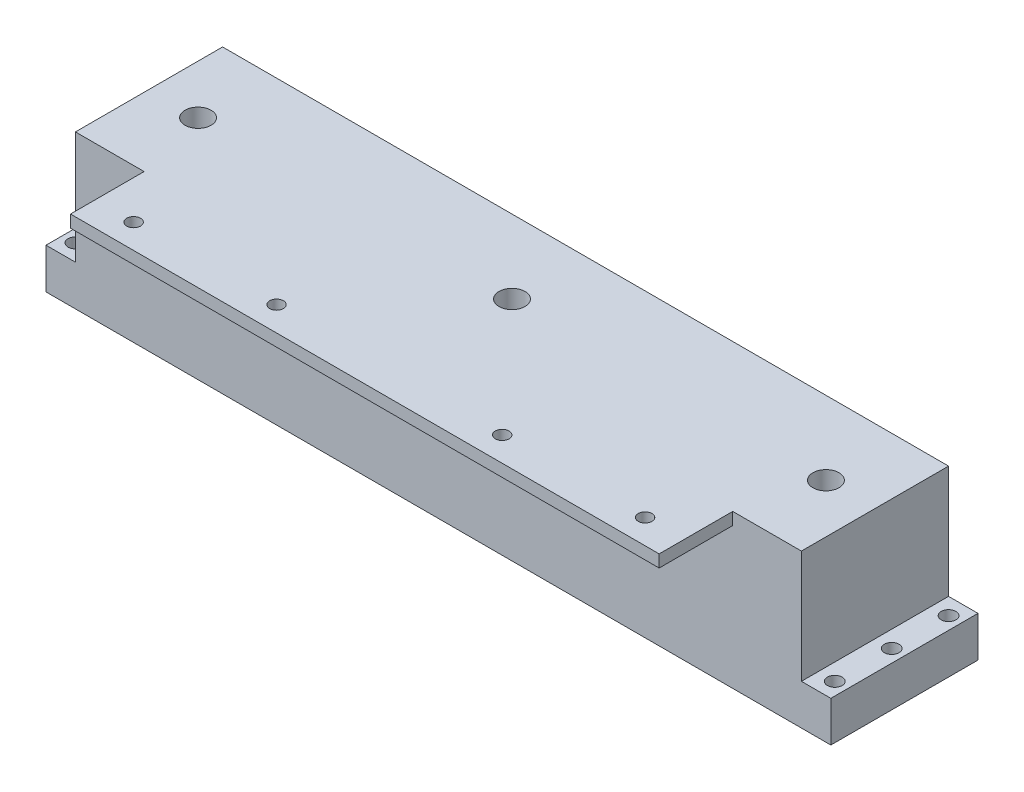
SolidWorks part; units mm, degrees
material "PPE"
ref_plane "Front Plane" through (0, 0, 0) normal (0, 0, 1) x (1, 0, 0)
ref_plane "Top Plane" through (0, 0, 0) normal (0, 1, 0) x (1, 0, 0)
ref_plane "Right Plane" through (0, 0, 0) normal (1, 0, 0) x (0, 0, -1)
sketch "Sketch1" plane through (0, 0, 0) normal (0, 1, 0) x (1, 0, 0)
  line L1 (-101.6, -19.05) -> (101.6, -19.05)
  line L2 (-101.6, -19.05) -> (-101.6, 19.05)
  line L3 (-101.6, 19.05) -> (101.6, 19.05)
  line L4 (101.6, -19.05) -> (101.6, 19.05)
  line L5 (-101.6, -19.05) -> (101.6, 19.05) construction
  line L6 (-101.6, 19.05) -> (101.6, -19.05) construction
  point P0 (0, 0)
  dimension "D1" = 203.2
  dimension "D2" = 38.1
extrude "Boss-Extrude1" add sketch "Sketch1" along normal blind 39.6926
sketch "Sketch3" plane through (0, 0, 0) normal (0, -1, 0) x (1, 0, 0)
  line L0 (-101.6, 0) -> (-60.6691, 0) construction
  line L1 (-101.6, -19.05) -> (-101.6, 19.05) construction
  line L2 (-98.298, 19.05) -> (-98.298, -19.05) construction
  line L3 (-101.6, 19.05) -> (101.6, 19.05) construction
  line L4 (101.6, -19.05) -> (-101.6, -19.05) construction
  circle A0 centre (-98.298, 14.732) radius 1.905
  circle A1 centre (-98.298, 0) radius 1.905
  circle A2 centre (-98.298, -14.732) radius 1.905
  dimension "D2" = 3.81
  dimension "D3" = 3.81
  dimension "D5" = 3.81
  dimension "D1" = 14.732
  dimension "D4" = 3.302
  dimension "D6" = 14.732
extrude "Cut-Extrude1" cut sketch "Sketch3" against normal through all
mirror "Mirror1" about plane through (0, 0, 0) normal (1, 0, 0) of "Cut-Extrude1"
sketch "Sketch4" plane through (0, 39.6926, 0) normal (0, 1, 0) x (1, 0, 0)
  line L0 (101.6, -19.05) -> (101.6, 19.05) construction
  line L1 (101.6, 19.05) -> (-101.6, 19.05) construction
  line L2 (0, 0) -> (0, -19.05) construction
  circle A1 centre (0, 0) radius 3.3782
  circle A2 centre (81.28, 0) radius 3.3782
  circle A3 centre (-81.28, 0) radius 3.3782
  dimension "D1" = 101.6
  dimension "D2" = 6.7564
  dimension "D5" = 6.7564
  dimension "D3" = 20.32
  dimension "D4" = 19.05
  dimension "D6" = 19.05
extrude "Cut-Extrude3" cut sketch "Sketch4" against normal through all
sketch "Sketch6" plane through (0, 0, 0) normal (0, -1, 0) x (1, 0, 0)
  line L0 (0, 19.05) -> (0, -19.05) construction
  line L1 (-101.6, 19.05) -> (101.6, 19.05) construction
  line L2 (101.6, -19.05) -> (-101.6, -19.05) construction
  line L3 (101.6, 19.05) -> (101.6, -19.05) construction
  line L4 (86.995, 3.2996) -> (81.28, 6.5991)
  line L5 (81.28, 6.5991) -> (75.565, 3.2996)
  line L6 (75.565, 3.2996) -> (75.565, -3.2996)
  line L7 (75.565, -3.2996) -> (81.28, -6.5991)
  line L8 (81.28, -6.5991) -> (86.995, -3.2996)
  line L9 (86.995, -3.2996) -> (86.995, 3.2996)
  line L10 (-86.995, -3.2996) -> (-86.995, 3.2996)
  line L11 (-81.28, -6.5991) -> (-86.995, -3.2996)
  line L12 (-75.565, -3.2996) -> (-81.28, -6.5991)
  line L13 (-75.565, 3.2996) -> (-75.565, -3.2996)
  line L14 (-81.28, 6.5991) -> (-75.565, 3.2996)
  line L15 (-86.995, 3.2996) -> (-81.28, 6.5991)
  line L16 (-101.6, -19.05) -> (-101.6, 19.05) construction
  line L17 (5.715, 3.2996) -> (0, 6.5991)
  line L18 (0, 6.5991) -> (-5.715, 3.2996)
  line L19 (-5.715, 3.2996) -> (-5.715, -3.2996)
  line L20 (-5.715, -3.2996) -> (0, -6.5991)
  line L21 (0, -6.5991) -> (5.715, -3.2996)
  line L22 (5.715, -3.2996) -> (5.715, 3.2996)
  circle A2 centre (81.28, 0) radius 5.715 construction
  circle A3 centre (0, 0) radius 5.715 construction
  dimension "D1" = 11.43
extrude "Cut-Extrude5" cut sketch "Sketch6" against normal blind 6.35
sketch "Sketch7" plane through (0, 39.6926, 0) normal (0, 1, 0) x (1, 0, 0)
  line L0 (-101.6, -19.05) -> (101.6, -19.05) construction
  line L1 (-101.6, 19.05) -> (-93.98, 19.05)
  line L2 (-101.6, 19.05) -> (-101.6, -19.05)
  line L3 (-101.6, -19.05) -> (-93.98, -19.05)
  line L4 (-93.98, 19.05) -> (-93.98, -19.05)
  line L5 (-101.6, 19.05) -> (-101.6, -19.05) construction
  line L6 (0, 19.05) -> (0, -19.05) construction
  line L7 (101.6, 19.05) -> (-101.6, 19.05) construction
  line L8 (101.6, -19.05) -> (93.98, -19.05)
  line L9 (93.98, 19.05) -> (93.98, -19.05)
  line L10 (101.6, 19.05) -> (93.98, 19.05)
  line L11 (101.6, 19.05) -> (101.6, -19.05)
  dimension "D1" = 7.62
extrude "Cut-Extrude6" cut sketch "Sketch7" against normal blind 29.21
sketch "Sketch8" plane through (0, 39.6926, 0) normal (0, 1, 0) x (1, 0, 0)
  line L0 (-93.98, -19.05) -> (93.98, -19.05) construction
  line L1 (-76.2, -19.05) -> (76.2, -19.05)
  line L2 (-76.2, -19.05) -> (-76.2, -38.1)
  line L3 (-76.2, -38.1) -> (76.2, -38.1)
  line L4 (76.2, -19.05) -> (76.2, -38.1)
  line L5 (-76.2, -19.05) -> (76.2, -38.1) construction
  line L6 (-76.2, -38.1) -> (76.2, -19.05) construction
  line L7 (0, 19.05) -> (0, -19.05) construction
  line L8 (93.98, 19.05) -> (-93.98, 19.05) construction
  point P0 (0, -28.575)
  dimension "D1" = 152.4
  dimension "D2" = 19.05
extrude "Boss-Extrude2" add sketch "Sketch8" against normal blind 3.175
sketch "Sketch9" plane through (0, 36.5176, 0) normal (0, -1, 0) x (1, 0, 0)
  line L0 (0, 38.1) -> (0, 0) construction
  line L1 (-76.2, 38.1) -> (76.2, 38.1) construction
  line L2 (76.2, 31.75) -> (52.2097, 31.75) construction
  line L4 (76.2, 38.1) -> (76.2, 19.05) construction
  circle A0 centre (29.21, 31.75) radius 1.778
  circle A1 centre (66.2102, 31.75) radius 1.778
  dimension "D2" = 3.556
  dimension "D4" = 6.35
  dimension "D1" = 29.21
  dimension "D3" = 37.0002
extrude "Cut-Extrude7" cut sketch "Sketch9" against normal up to next (3.175 mm away)
mirror "Mirror2" about plane through (0, 0, 0) normal (1, 0, 0) of "Cut-Extrude7"
sketch "Sketch10" plane through (0, 0, 19.05) normal (0, 0, 1) x (1, 0, 0)
  line L0 (76.2, 36.5176) -> (76.2, 4.1178) construction
  line L1 (58.42, 36.5176) -> (38.1, 36.5176)
  line L2 (58.42, 36.5176) -> (58.42, 23.8176)
  line L3 (58.42, 23.8176) -> (38.1, 23.8176)
  line L4 (38.1, 36.5176) -> (38.1, 23.8176)
  line L5 (76.2, 36.5176) -> (-76.2, 36.5176) construction
  dimension "D1" = 12.7
  dimension "D2" = 20.32
  dimension "D3" = 17.78
extrude "Cut-Extrude8" cut sketch "Sketch10" against normal up to next (38.1 mm away)
mirror "Mirror3" about plane through (0, 0, 0) normal (1, 0, 0) of "Cut-Extrude8"
scale "Scale1" scale about centroid uniform scaling yes scale factor 1.02
